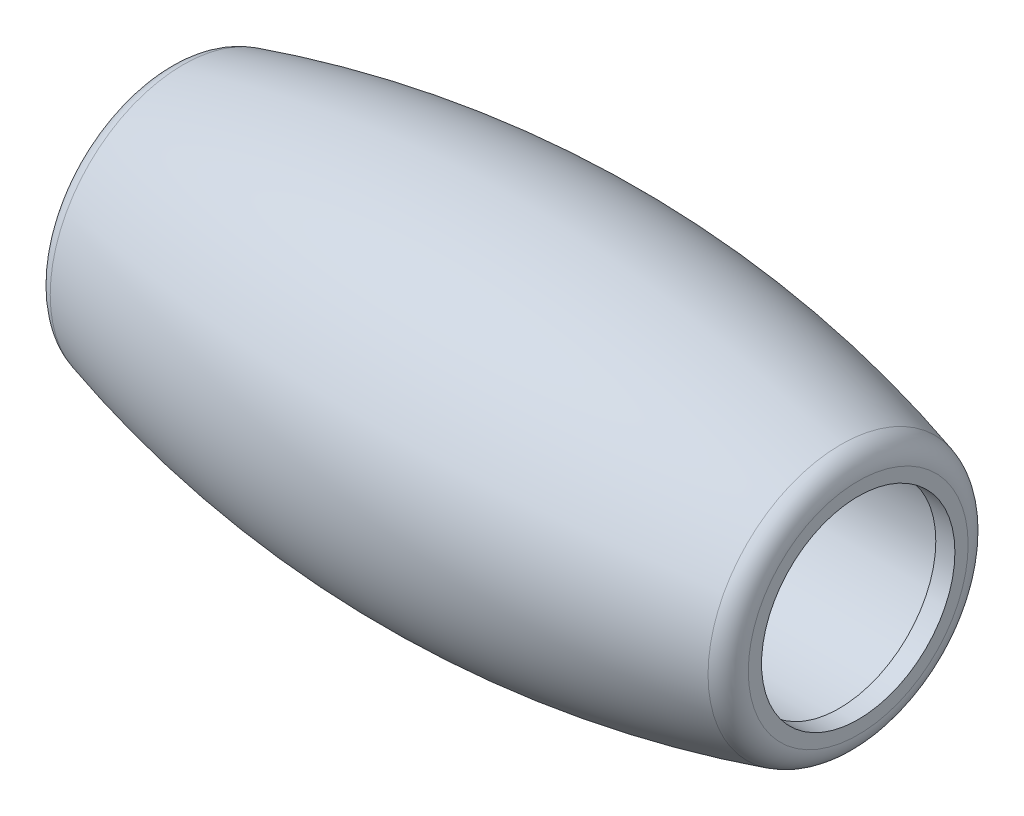
SolidWorks part; units mm, degrees
material "Rubber"
ref_plane "Front Plane" through (0, 0, 0) normal (0, 0, 1) x (1, 0, 0)
ref_plane "Top Plane" through (0, 0, 0) normal (0, 1, 0) x (1, 0, 0)
ref_plane "Right Plane" through (0, 0, 0) normal (1, 0, 0) x (0, 0, -1)
sketch "Sketch1" plane through (0, 0, 0) normal (0, 1, 0) x (1, 0, 0)
  line L0 (0, 42.5) -> (0, -7.5) construction
  line L1 (15, 0) -> (-15, 0) construction
  line L2 (15, 5.197) -> (15, -5.197)
  line L3 (-15, 5.197) -> (-15, -5.197)
  line L4 (-24.8054, 10.8581) -> (-33.8068, 5.6611)
  line L5 (-39.8054, 36.8389) -> (-48.8068, 31.6419)
  line L6 (-29.3061, 8.2596) -> (-44.3061, 34.2404) construction
  line L7 (-39.8054, 48.1611) -> (-48.8068, 53.3581)
  line L8 (-24.8054, 74.1419) -> (-33.8068, 79.3389)
  line L9 (-44.3061, 50.7596) -> (-29.3061, 76.7404) construction
  line L10 (-15, 79.803) -> (-15, 90.197)
  line L11 (15, 79.803) -> (15, 90.197)
  line L12 (-15, 85) -> (15, 85) construction
  line L13 (24.8054, 74.1419) -> (33.8068, 79.3389)
  line L14 (39.8054, 48.1611) -> (48.8068, 53.3581)
  line L15 (29.3061, 76.7404) -> (44.3061, 50.7596) construction
  line L16 (39.8054, 36.8389) -> (48.8068, 31.6419)
  line L17 (24.8054, 10.8581) -> (33.8068, 5.6611)
  line L18 (44.3061, 34.2404) -> (29.3061, 8.2596) construction
  line L19 (-16.5, 6.2852) -> (-16.5, -5.197)
  line L20 (16.5, 6.2852) -> (16.5, -5.197)
  circle A0 centre (0, 42.5) radius 50
  circle A1 centre (0, 42.5) radius 42.5 construction
  arc A2 (-15, 5.197) -> (15, 5.197) centre (0, -42.5) cw
  arc A3 (-39.8054, 36.8389) -> (-24.8054, 10.8581) centre (-73.6122, 0) cw
  arc A4 (-24.8054, 74.1419) -> (-39.8054, 48.1611) centre (-73.6122, 85) cw
  arc A5 (15, 79.803) -> (-15, 79.803) centre (0, 127.5) cw
  arc A6 (39.8054, 48.1611) -> (24.8054, 74.1419) centre (73.6122, 85) cw
  arc A7 (24.8054, 10.8581) -> (39.8054, 36.8389) centre (73.6122, 0) cw
  circle A8 centre (0, 42.5) radius 33.5
  circle A9 centre (0, 42.5) radius 28
  arc A10 (-16.5, 6.2852) -> (16.5, 6.2852) centre (0, -42.5) cw
  circle A11 centre (0, 42.5) radius 31
  point P15 (0, 0)
  point P25 (-36.8061, 21.25)
  point P33 (-36.8061, 63.75)
  point P41 (0, 85)
  point P49 (36.8061, 63.75)
  point P57 (36.8061, 21.25)
  point P62 (0, 42.5)
  dimension "D1" = 30
sketch "Sketch2" plane through (0, 0, 0) normal (0, 1, 0) x (1, 0, 0)
  line L0 (15, 0) -> (-15, 0) construction
  line L1 (15, 0) -> (-15, 0) construction
  line L2 (-17.4568, 3.5) -> (17.304, 3.5) construction
  line L3 (-16.2311, 4.05) -> (17.6962, 4.05) construction
  line L4 (-14.5, 5.197) -> (-14.5, -5.197)
  line L5 (-14.5, 5.197) -> (-14.5, -5.197) construction
  line L7 (14.5, 5.197) -> (14.5, -5.197)
  line L8 (14.5, 5.197) -> (14.5, -5.197) construction
  line L9 (-14.5, 5.3513) -> (-14.5, 4.05)
  line L10 (0, 2) -> (0, 0) construction
  line L12 (14.5, 4.05) -> (14.5, 5.3513)
  line L13 (-14.5, 4.05) -> (-13.7, 4.05)
  line L14 (0, 42.5) -> (0, -7.5) construction
  line L15 (-14.5, 5.197) -> (-14.5, -5.197) construction
  line L16 (-13.7, 4.05) -> (-13.7, 4.5)
  line L17 (-13.7, 4.5) -> (13.7, 4.5)
  line L18 (13.7, 4.5) -> (13.7, 4.05)
  line L19 (13.7, 4.05) -> (14.5, 4.05)
  arc A0 (15, 5.197) -> (-15, 5.197) centre (0, -42.5) ccw construction
  arc A1 (14.5, 5.3513) -> (-14.5, 5.3513) centre (0, -42.5) ccw
  dimension "D3" = 3.5
  dimension "D4" = 4.05
  dimension "D5" = 0.8
  dimension "D6" = 0.8
  dimension "D7" = 4.5
  dimension "D1" = 0.5
  dimension "D2" = 0.5
revolve "Revolve1" add sketch "Sketch2" angle 360 about L1
fillet "Fillet1" radius 1 2 edges at (14.5, 0, -5.3513) (-14.5, 0, -5.3513)
